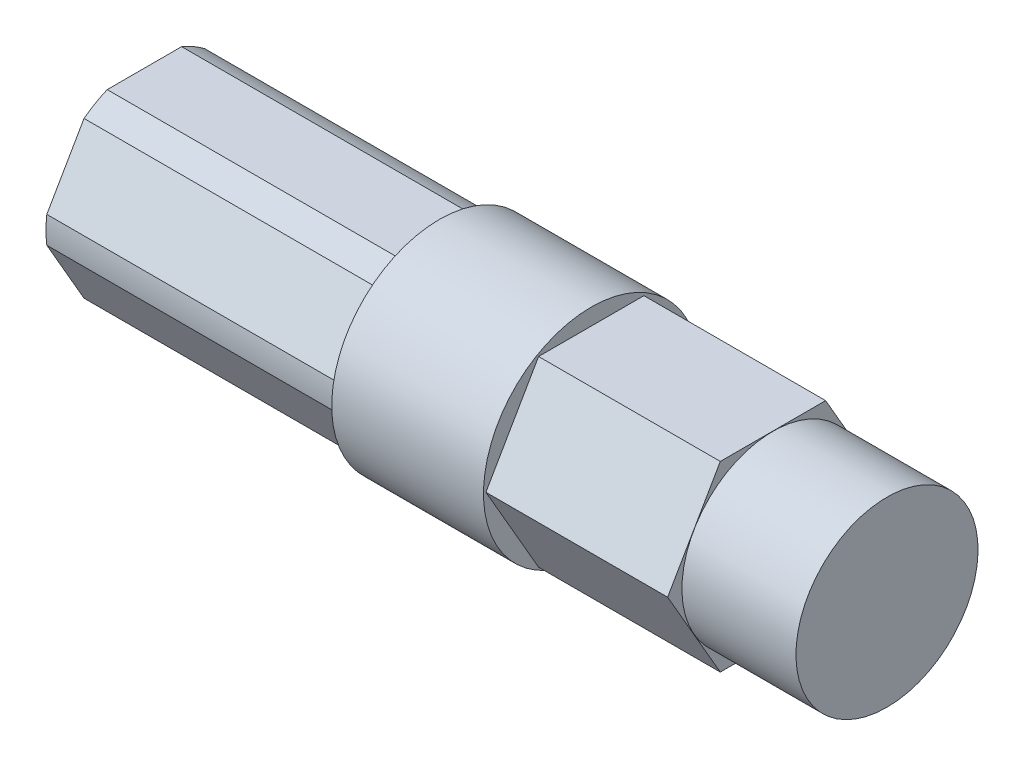
SolidWorks part; units mm, degrees
ref_plane "Front Plane" through (0, 0, 0) normal (0, 0, 1) x (1, 0, 0)
ref_plane "Top Plane" through (0, 0, 0) normal (0, 1, 0) x (1, 0, 0)
ref_plane "Right Plane" through (0, 0, 0) normal (1, 0, 0) x (0, 0, -1)
sketch "Sketch1" plane through (0, 0, 0) normal (0, 0, 1) x (1, 0, 0)
  line L0 (-1.3398, 7.5) -> (-1.3398, 0)
  line L1 (-1.3398, 0) -> (9.2265, 0)
  line L2 (9.2265, 0) -> (9.2265, 7.5)
  line L3 (9.2265, 7.5) -> (-1.3398, 7.5)
  line L4 (-1.3398, 0) -> (9.2265, 0) construction
revolve "Revolve1" add sketch "Sketch1" angle 360 about L4
sketch "Sketch2" plane through (-1.3398, 0, 0) normal (-1, 0, 0) x (0, 0, 1)
  line L0 (-2.5903, 6.35) -> (2.5903, 6.35)
  line L1 (4.2041, 5.4183) -> (6.7944, 0.9317)
  line L2 (6.7944, -0.9317) -> (4.2041, -5.4183)
  line L3 (2.5903, -6.35) -> (-2.5903, -6.35)
  line L4 (-4.2041, -5.4183) -> (-6.7944, -0.9317)
  line L5 (-6.7944, 0.9317) -> (-4.2041, 5.4183)
  arc A0 (2.5903, 6.35) -> (4.2041, 5.4183) centre (0, 0) cw
  arc A1 (6.7944, 0.9317) -> (6.7944, -0.9317) centre (0, 0) cw
  arc A2 (4.2041, -5.4183) -> (2.5903, -6.35) centre (0, 0) cw
  arc A3 (-2.5903, -6.35) -> (-4.2041, -5.4183) centre (0, 0) cw
  arc A4 (-6.7944, -0.9317) -> (-6.7944, 0.9317) centre (0, 0) cw
  arc A5 (-4.2041, 5.4183) -> (-2.5903, 6.35) centre (0, 0) cw
extrude "Boss-Extrude1" add sketch "Sketch2" along normal blind 20.5359
sketch "Sketch3" plane through (9.2265, 0, 0) normal (1, 0, 0) x (0, 0, -1)
  line L0 (3.6662, -6.35) -> (-3.6662, -6.35)
  line L1 (-3.6662, -6.35) -> (-7.3323, 0)
  line L2 (-7.3323, 0) -> (-3.6662, 6.35)
  line L3 (-3.6662, 6.35) -> (3.6662, 6.35)
  line L4 (3.6662, 6.35) -> (7.3323, 0)
  line L5 (7.3323, 0) -> (3.6662, -6.35)
extrude "Boss-Extrude2" add sketch "Sketch3" along normal blind 12.6492
ref_plane "Plane1" through (0, 0, 0) normal (0, 0, -1) x (-1, 0, 0)
sketch "Sketch4" plane through (0, 0, 0) normal (0, 0, -1) x (-1, 0, 0)
  line L0 (-29.8132, 6.3373) -> (-29.8132, 0)
  line L1 (-29.8132, 0) -> (-21.8757, 0)
  line L2 (-21.8757, 0) -> (-21.8757, 6.3373)
  line L3 (-21.8757, 6.3373) -> (-29.8132, 6.3373)
  line L4 (-29.8132, 0) -> (-21.8757, 0) construction
revolve "Revolve2" add sketch "Sketch4" angle 360 about L4
hole_wizard "#21 (0.159) Diameter Hole1" positions "Sketch6" profile "Sketch5" hole size "#21" standard "ANSI Inch"
sketch "Sketch6" plane through (-21.8757, 0, 0) normal (-1, 0, 0) x (0, 0, 1)
  point P0 (0, 0)
sketch "Sketch5" plane through (-21.8757, 0, 0) normal (0, 1, 0) x (0, 0, 1)
  line L0 (0, 0) -> (0, 17.0883)
  line L1 (0, 17.0883) -> (2.0193, 15.875)
  line L2 (2.0193, 15.875) -> (2.0193, 0)
  line L5 (2.0193, 0) -> (0, 0)
  line L10 (0, 17.0883) -> (-2.0193, 15.875) construction
  line L11 (0, -6.35) -> (0, 107.95) construction
  dimension "Hole Dia." = 4.0386
  dimension "Hole Depth" = 15.875
  dimension "Drill Angle" = 118
sketch "Sketch7" plane through (-21.8757, 0, 0) normal (-1, 0, 0) x (0, 0, 1)
  circle A0 centre (0, 0) radius 3.175
  dimension "D1" = 6.35
extrude "Cut-Extrude1" cut sketch "Sketch7" against normal blind 12.7
